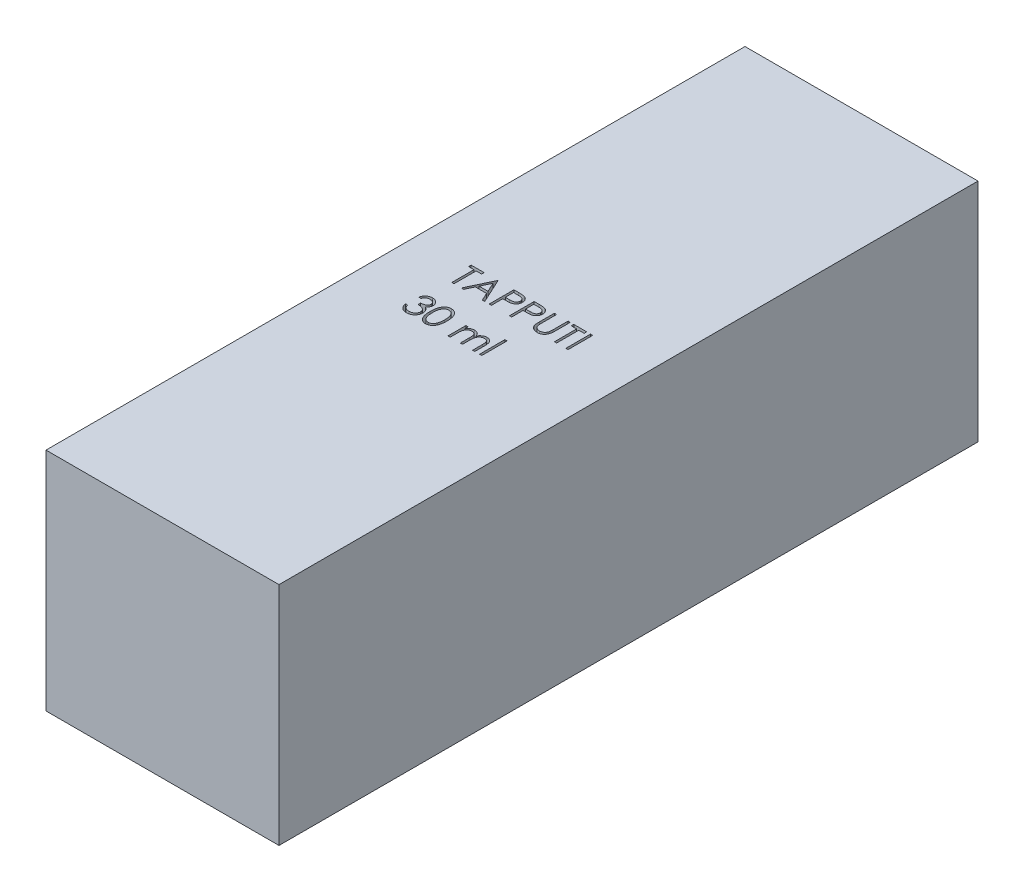
SolidWorks part; units mm, degrees
ref_plane "Front Plane" through (0, 0, 0) normal (0, 0, 1) x (1, 0, 0)
ref_plane "Top Plane" through (0, 0, 0) normal (0, 1, 0) x (1, 0, 0)
ref_plane "Right Plane" through (0, 0, 0) normal (1, 0, 0) x (0, 0, -1)
sketch "Sketch1" plane through (0, 0, 0) normal (0, 1, 0) x (1, 0, 0)
  line L1 (-16.5, 49.5) -> (16.5, 49.5)
  line L2 (-16.5, 49.5) -> (-16.5, -49.5)
  line L3 (-16.5, -49.5) -> (16.5, -49.5)
  line L4 (16.5, 49.5) -> (16.5, -49.5)
  line L5 (-16.5, 49.5) -> (16.5, -49.5) construction
  line L6 (-16.5, -49.5) -> (16.5, 49.5) construction
  point P0 (0, 0)
  dimension "D1" = 33
  dimension "D2" = 99
extrude "Boss-Extrude1" add sketch "Sketch1" along normal blind 32
sketch "Sketch2" plane through (0, 32, 0) normal (0, 1, 0) x (1, 0, 0)
  text T0 "TAPPUTI\r\n30 ml"
extrude "Cut-Extrude1" cut sketch "Sketch2" against normal blind 10
